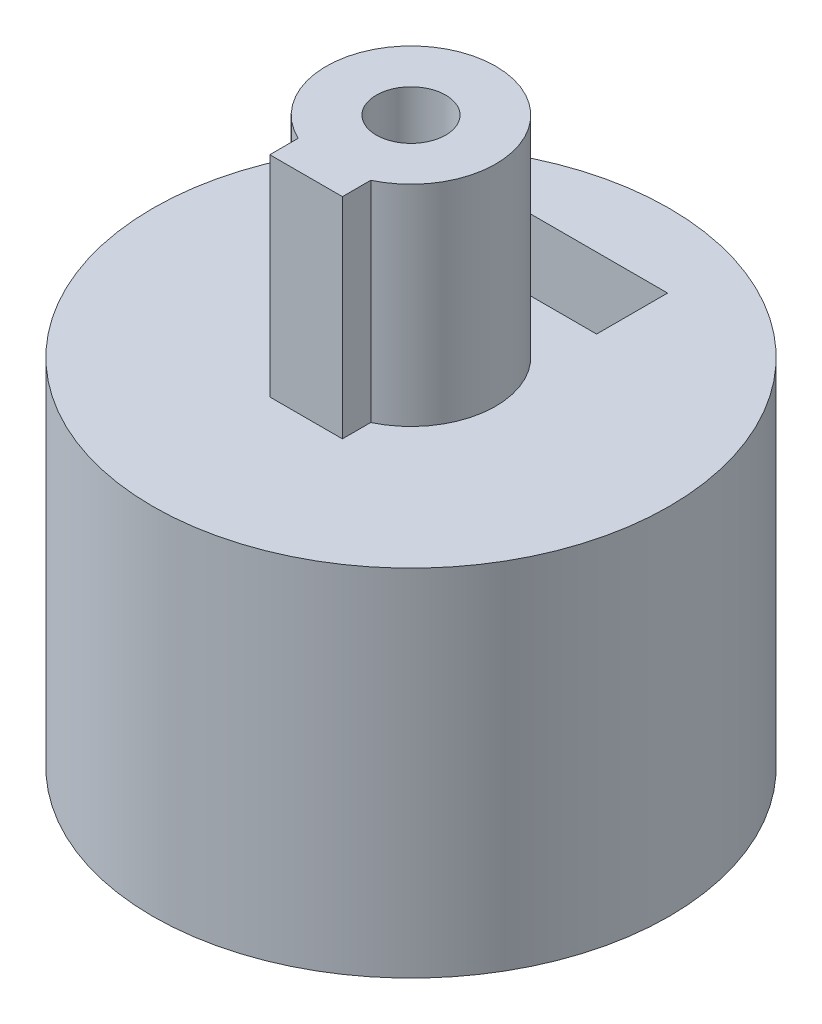
SolidWorks part; units mm, degrees
ref_plane "Front Plane" through (0, 0, 0) normal (0, 0, 1) x (1, 0, 0)
ref_plane "Top Plane" through (0, 0, 0) normal (0, 1, 0) x (1, 0, 0)
ref_plane "Right Plane" through (0, 0, 0) normal (1, 0, 0) x (0, 0, -1)
sketch "Sketch1" plane through (0, 0, 0) normal (0, 1, 0) x (1, 0, 0)
  circle A0 centre (0, 0) radius 1.965 construction
  circle A1 centre (0, 0) radius 8
  dimension "D1" = 3.93
  dimension "D2" = 16
extrude "Boss-Extrude1" add sketch "Sketch1" along normal blind 10
sketch "Sketch2" plane through (0, 0, 0) normal (0, 0, 1) x (1, 0, 0)
  line L0 (0, 10) -> (0, 0) construction
  line L1 (8, 10) -> (-8, 10) construction
  circle A0 centre (0, 7) radius 1.075
  dimension "D1" = 2.15
  dimension "D2" = 3
extrude "Cut-Extrude1" cut sketch "Sketch2" against normal through all
sketch "Sketch4" plane through (0, 0, 0) normal (0, 1, 0) x (1, 0, 0)
  circle A0 centre (0, 0) radius 2.275
  dimension "D1" = 4.55
extrude "Cut-Extrude4" cut sketch "Sketch4" along normal through all
sketch "Sketch5" plane through (0, 10, 0) normal (0, 1, 0) x (1, 0, 0)
  line L0 (-8, 0) -> (8, 0) construction
  line L2 (-0.475, -3.5346) -> (0.475, -3.5346)
  line L3 (-0.475, -3.5346) -> (-0.475, 3.5346)
  line L4 (-0.475, 3.5346) -> (0.475, 3.5346)
  line L5 (0.475, -3.5346) -> (0.475, 3.5346)
  line L6 (0, 3.5346) -> (0, -3.5346) construction
  line L7 (-0.475, 0) -> (0.475, 0) construction
  circle A0 centre (0, 0) radius 8 construction
  point P5 (0, 0)
  dimension "D1" = 0.95
extrude "Boss-Extrude2" add sketch "Sketch5" against normal blind 1.2
sketch "Sketch7" plane through (0, 10, 0) normal (0, 1, 0) x (1, 0, 0)
  circle A0 centre (0, 0) radius 8
  circle A1 centre (0, 0) radius 8 construction
extrude "Boss-Extrude3" add sketch "Sketch7" along normal blind 1
sketch "Sketch8" plane through (0, 11, 0) normal (0, 1, 0) x (1, 0, 0)
  line L0 (0, 0) -> (0, -8) construction
  line L2 (-1.125, -2) -> (1.125, -2)
  line L3 (-1.125, -2) -> (-1.125, -3.25)
  line L4 (-1.125, -3.25) -> (1.125, -3.25)
  line L5 (1.125, -2) -> (1.125, -3.25)
  line L6 (0, -3.25) -> (0, -2) construction
  line L7 (-1.125, -2.625) -> (1.125, -2.625) construction
  circle A0 centre (0, 0) radius 2.625
  circle A1 centre (0, 0) radius 8 construction
  point P3 (0, -2.625)
  dimension "D1" = 5.25
  dimension "D2" = 3.25
  dimension "D3" = 2.25
extrude "Boss-Extrude4" add sketch "Sketch8" along normal blind 6.5 contours A0 L3 L4 L5
sketch "Sketch9" plane through (0, 17.5, 0) normal (0, 1, 0) x (1, 0, 0)
  circle A0 centre (0, 0) radius 1.075
  dimension "D1" = 2.15
extrude "Cut-Extrude5" cut sketch "Sketch9" against normal blind 6
sketch "Sketch3" plane through (0, 0, 0) normal (0, 0, 1) x (1, 0, 0)
  line L1 (0, 4.4019) -> (2.25, 5.701)
  line L2 (2.25, 5.701) -> (2.25, 8.299)
  line L3 (2.25, 8.299) -> (0, 9.5981) construction
  line L4 (0, 9.5981) -> (-2.25, 8.299) construction
  line L5 (-2.25, 8.299) -> (-2.25, 5.701)
  line L6 (-2.25, 5.701) -> (0, 4.4019)
  line L10 (-2.25, 8.299) -> (2.25, 8.299) construction
  line L11 (-2.25, 8.299) -> (-2.25, 11.4728)
  line L12 (2.25, 8.299) -> (2.25, 11.4728)
  line L13 (-2.25, 11.4728) -> (2.25, 11.4728)
  circle A0 centre (0, 7) radius 2.25 construction
  dimension "D1" = 4.5
extrude "Cut-Extrude2" cut sketch "Sketch3" against normal blind 2.2 from offset 3.5
